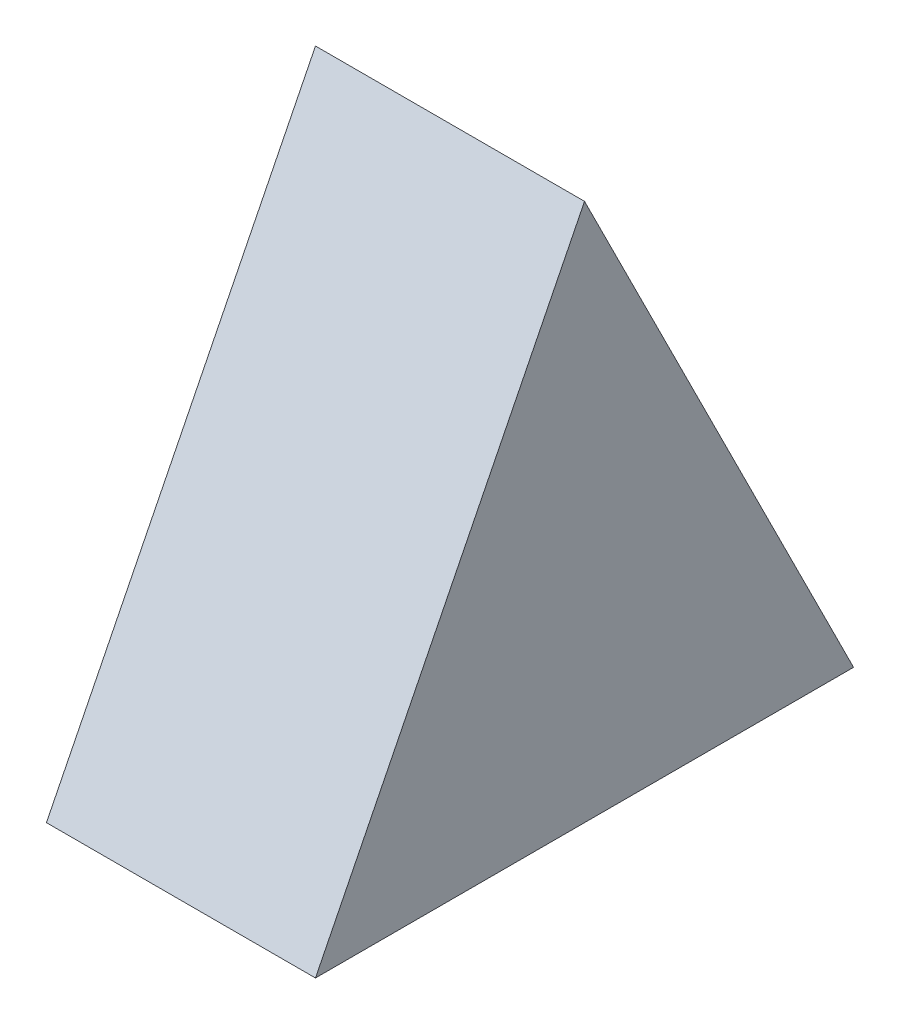
SolidWorks part; units mm, degrees
ref_plane "Front Plane" through (0, 0, 0) normal (0, 0, 1) x (1, 0, 0)
ref_plane "Top Plane" through (0, 0, 0) normal (0, 1, 0) x (1, 0, 0)
ref_plane "Right Plane" through (0, 0, 0) normal (1, 0, 0) x (0, 0, -1)
sketch "Sketch1" plane through (0, 0, 0) normal (0, 0, 1) x (1, 0, 0)
  line L1 (0, 0) -> (40, 0)
  line L2 (0, 0) -> (0, 40)
  line L3 (0, 40) -> (40, 40)
  line L4 (40, 0) -> (40, 40)
  dimension "D1" = 40
  dimension "D2" = 40
extrude "Boss-Extrude1" add sketch "Sketch1" along normal blind 40
sketch "Sketch2" plane through (0, 0, 40) normal (0, 0, 1) x (1, 0, 0)
  line L0 (0, 0) -> (20, 40)
  line L1 (40, 40) -> (0, 40) construction
  line L2 (20, 40) -> (0, 40)
  line L3 (0, 40) -> (0, 0)
extrude "Cut-Extrude1" cut sketch "Sketch2" against normal blind 40
sketch "Sketch3" plane through (0, 0, 0) normal (0, -1, 0) x (1, 0, 0)
  line L0 (0, 0) -> (20, 20)
  line L1 (20, 20) -> (20, 40)
  line L2 (0, 40) -> (40, 40) construction
  line L3 (20, 40) -> (0, 40)
  line L4 (0, 40) -> (0, 0)
  dimension "D1" = 20
  dimension "D2" = 20
extrude "Cut-Extrude2" cut sketch "Sketch3" against normal blind 40
sketch "Sketch4" plane through (20, 0, 0) normal (-1, 0, 0) x (0, 0, 1)
  line L0 (20, 40) -> (40, 0)
  line L1 (40, 0) -> (40, 40)
  line L2 (20, 40) -> (40, 40) construction
  line L3 (40, 40) -> (40, 0) construction
  line L4 (40, 40) -> (20, 40)
extrude "Cut-Extrude3" cut sketch "Sketch4" against normal blind 40
ref_plane "Plane1" through (0, 0, 0) normal (0, -0.4472, 0.8944) x (1, 0, 0)
sketch "Sketch5" plane through (0, 0, 0) normal (0, -0.4472, 0.8944) x (1, 0, 0)
  line L0 (0, 0) -> (40, 0)
  line L1 (40, 0) -> (40, 44.7214)
  line L2 (40, 44.7214) -> (20, 44.7214)
  line L3 (20, 44.7214) -> (0, 0)
extrude "Cut-Extrude4" cut sketch "Sketch5" against normal blind 40
